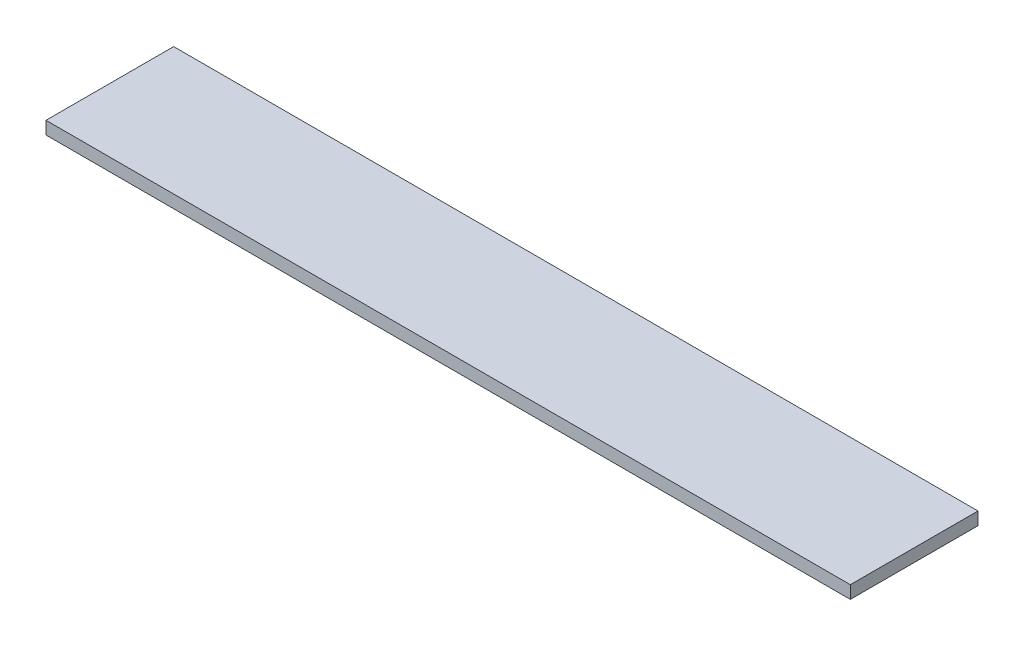
SolidWorks part; units mm, degrees
ref_plane "Front Plane" through (0, 0, 0) normal (0, 0, 1) x (1, 0, 0)
ref_plane "Top Plane" through (0, 0, 0) normal (0, 1, 0) x (1, 0, 0)
ref_plane "Right Plane" through (0, 0, 0) normal (1, 0, 0) x (0, 0, -1)
sketch "Sketch1" plane through (0, 0, 0) normal (0, 1, 0) x (1, 0, 0)
  line L1 (-40.005, -6.35) -> (40.005, -6.35)
  line L2 (-40.005, -6.35) -> (-40.005, 6.35)
  line L3 (-40.005, 6.35) -> (40.005, 6.35)
  line L4 (40.005, -6.35) -> (40.005, 6.35)
  line L5 (-40.005, -6.35) -> (40.005, 6.35) construction
  line L6 (-40.005, 6.35) -> (40.005, -6.35) construction
  point P0 (0, 0)
  dimension "D1" = 12.7
  dimension "D2" = 80.01
extrude "Boss-Extrude1" add sketch "Sketch1" along normal blind 1.27
